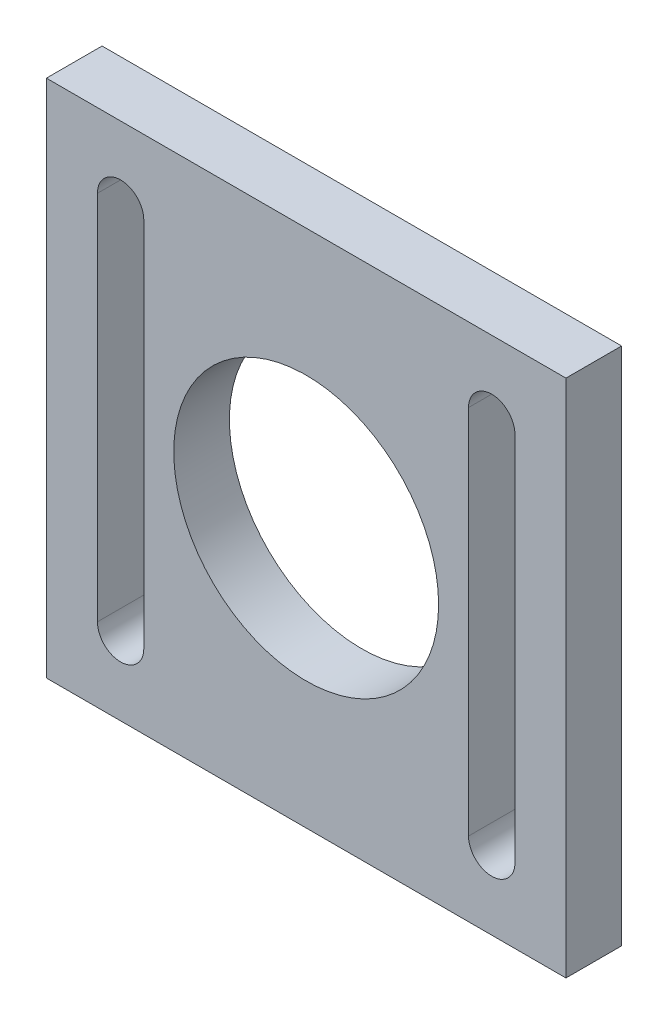
SolidWorks part; units mm, degrees
ref_plane "Front Plane" through (0, 0, 0) normal (0, 0, 1) x (1, 0, 0)
ref_plane "Top Plane" through (0, 0, 0) normal (0, 1, 0) x (1, 0, 0)
ref_plane "Right Plane" through (0, 0, 0) normal (1, 0, 0) x (0, 0, -1)
sketch "Sketch1" plane through (0, 0, 0) normal (0, 0, 1) x (1, 0, 0)
  line L1 (0, 0) -> (56, 0)
  line L2 (0, 0) -> (0, 56)
  line L3 (0, 56) -> (56, 56)
  line L4 (56, 0) -> (56, 56)
  dimension "D1" = 56
  dimension "D2" = 56
extrude "Boss-Extrude1" add sketch "Sketch1" along normal blind 6 contours L3 L4 L1 L2
sketch "Sketch2" plane through (0, 0, 6) normal (0, 0, 1) x (1, 0, 0)
  line L0 (28, 56) -> (28, 0) construction
  line L1 (0, 56) -> (56, 56) construction
  line L2 (0, 0) -> (56, 0) construction
  line L3 (0, 28) -> (56, 28) construction
  line L4 (0, 0) -> (0, 56) construction
  line L5 (56, 0) -> (56, 56) construction
  line L6 (8, 48) -> (8, 8) construction
  line L7 (10.5, 48) -> (10.5, 8)
  line L8 (5.5, 48) -> (5.5, 8)
  line L9 (48, 48) -> (48, 8) construction
  line L10 (50.5, 48) -> (50.5, 8)
  line L11 (45.5, 48) -> (45.5, 8)
  circle A0 centre (28, 28) radius 14.275
  arc A5 (10.5, 48) -> (5.5, 48) centre (8, 48) ccw
  arc A6 (5.5, 8) -> (10.5, 8) centre (8, 8) ccw
  arc A7 (50.5, 48) -> (45.5, 48) centre (48, 48) ccw
  arc A8 (45.5, 8) -> (50.5, 8) centre (48, 8) ccw
  point P22 (8, 28)
  point P27 (48, 28)
  dimension "D1" = 28.55
  dimension "D6" = 8
  dimension "D7" = 8
  dimension "D8" = 8
  dimension "D9" = 8
  dimension "D10" = 8
  dimension "D11" = 8
  dimension "D12" = 8
  dimension "D13" = 8
  dimension "D14" = 5
  dimension "D15" = 5
extrude "Cut-Extrude1" cut sketch "Sketch2" against normal blind 6
